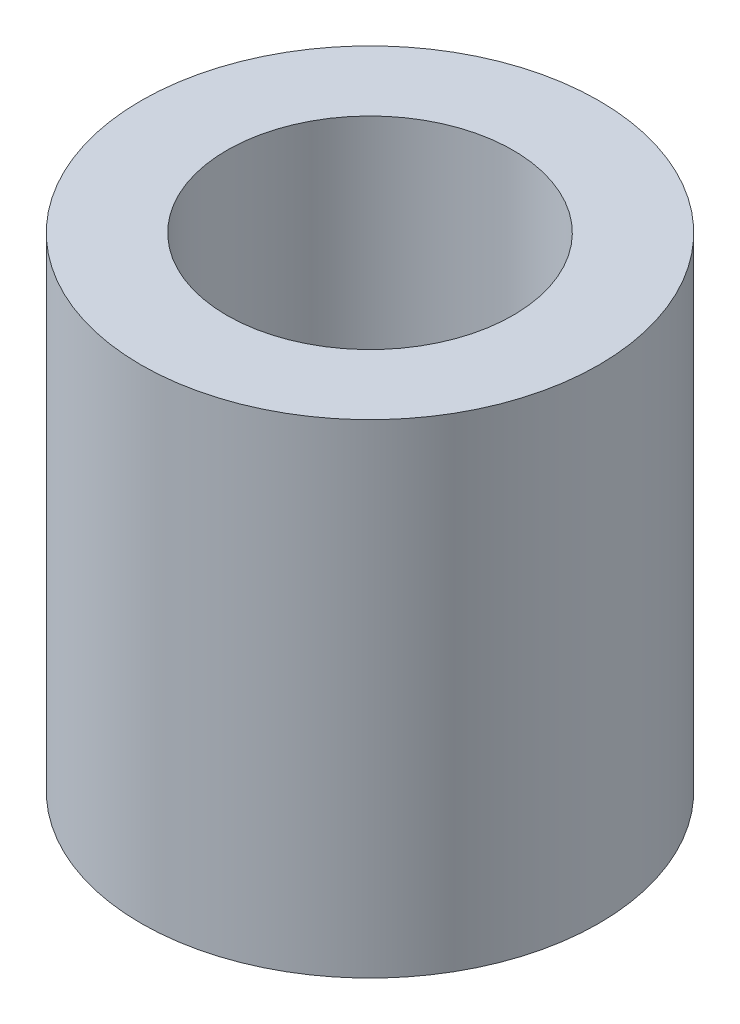
SolidWorks part; units mm, degrees
ref_plane "Front Plane" through (0, 0, 0) normal (0, 0, 1) x (1, 0, 0)
ref_plane "Top Plane" through (0, 0, 0) normal (0, 1, 0) x (1, 0, 0)
ref_plane "Right Plane" through (0, 0, 0) normal (1, 0, 0) x (0, 0, -1)
sketch "Sketch1" plane through (0, 0, 0) normal (0, 1, 0) x (1, 0, 0)
  circle A0 centre (0, 0) radius 2.5
  circle A1 centre (0, 0) radius 4
  dimension "D1" = 8
  dimension "D2" = 5
extrude "Boss-Extrude1" add sketch "Sketch1" along normal blind 8.45
